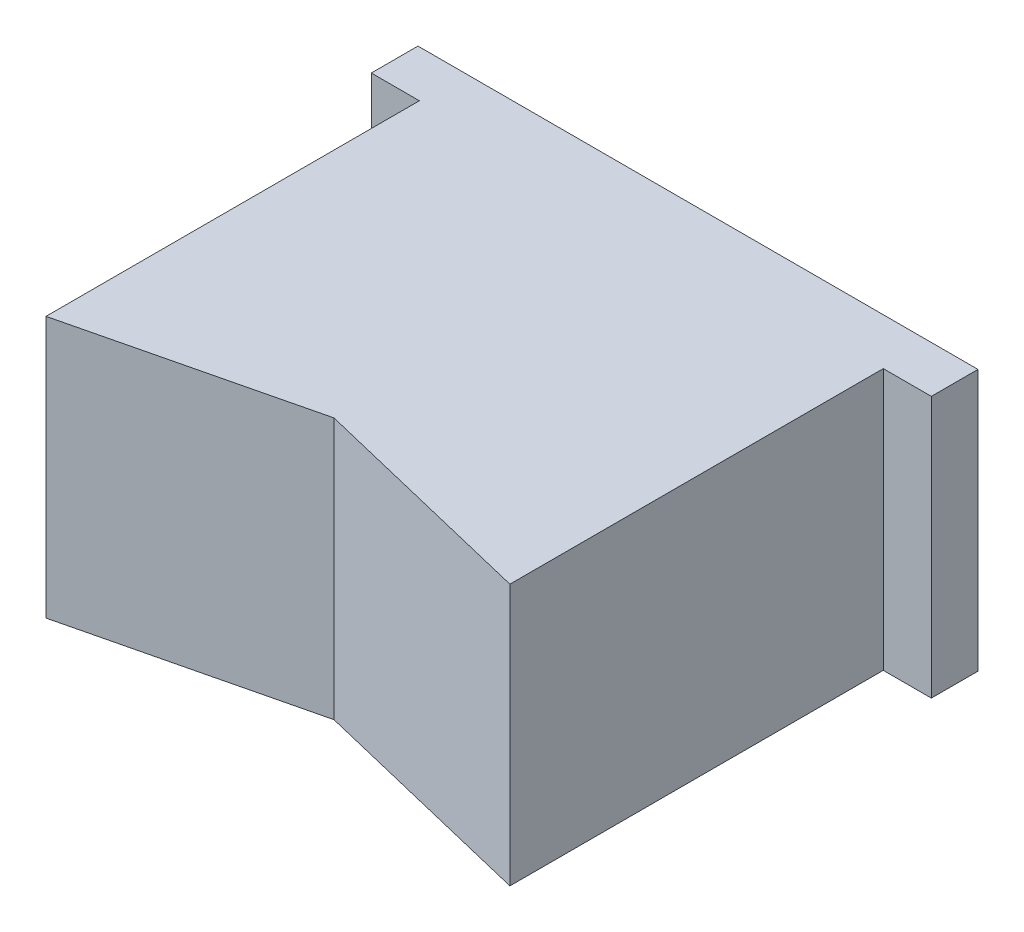
SolidWorks part; units mm, degrees
ref_plane "Alzado" through (0, 0, 0) normal (0, 0, 1) x (1, 0, 0)
ref_plane "Planta" through (0, 0, 0) normal (0, 1, 0) x (1, 0, 0)
ref_plane "Vista lateral" through (0, 0, 0) normal (1, 0, 0) x (0, 0, -1)
sketch "Croquis1" plane through (0, 0, 0) normal (0, 0, 1) x (1, 0, 0)
  line L1 (-15, 7) -> (15, 7)
  line L2 (-15, 7) -> (-15, -7)
  line L3 (-15, -7) -> (15, -7)
  line L4 (15, 7) -> (15, -7)
  line L5 (-15, 7) -> (15, -7) construction
  line L6 (-15, -7) -> (15, 7) construction
  point P0 (0, 0)
  dimension "D1" = 14
  dimension "D2" = 30
extrude "Saliente-Extruir1" add sketch "Croquis1" along normal blind 2.5
sketch "Croquis2" plane through (0, 0, 2.5) normal (0, 0, 1) x (1, 0, 0)
  line L1 (-12.425, 7) -> (12.425, 7)
  line L2 (-12.425, 7) -> (-12.425, -7)
  line L3 (-12.425, -7) -> (12.425, -7)
  line L4 (12.425, 7) -> (12.425, -7)
  line L5 (-12.425, 7) -> (12.425, -7) construction
  line L6 (-12.425, -7) -> (12.425, 7) construction
  point P0 (0, 0)
  dimension "D1" = 24.85
  dimension "D2" = 14
extrude "Saliente-Extruir2" add sketch "Croquis2" along normal blind 20
sketch "Croquis4" plane through (0, 7, 0) normal (0, 1, 0) x (1, 0, 0)
  line L0 (-12.425, -22.5) -> (0, -19.5)
  line L1 (0, -19.5) -> (12.425, -22.5)
  line L3 (12.425, -22.5) -> (-12.425, -22.5) construction
  line L4 (-12.425, -22.5) -> (12.425, -22.5)
  point P7 (0, -22.5)
  dimension "D1" = 3
extrude "Cortar-Extruir1" cut sketch "Croquis4" against normal blind 20
